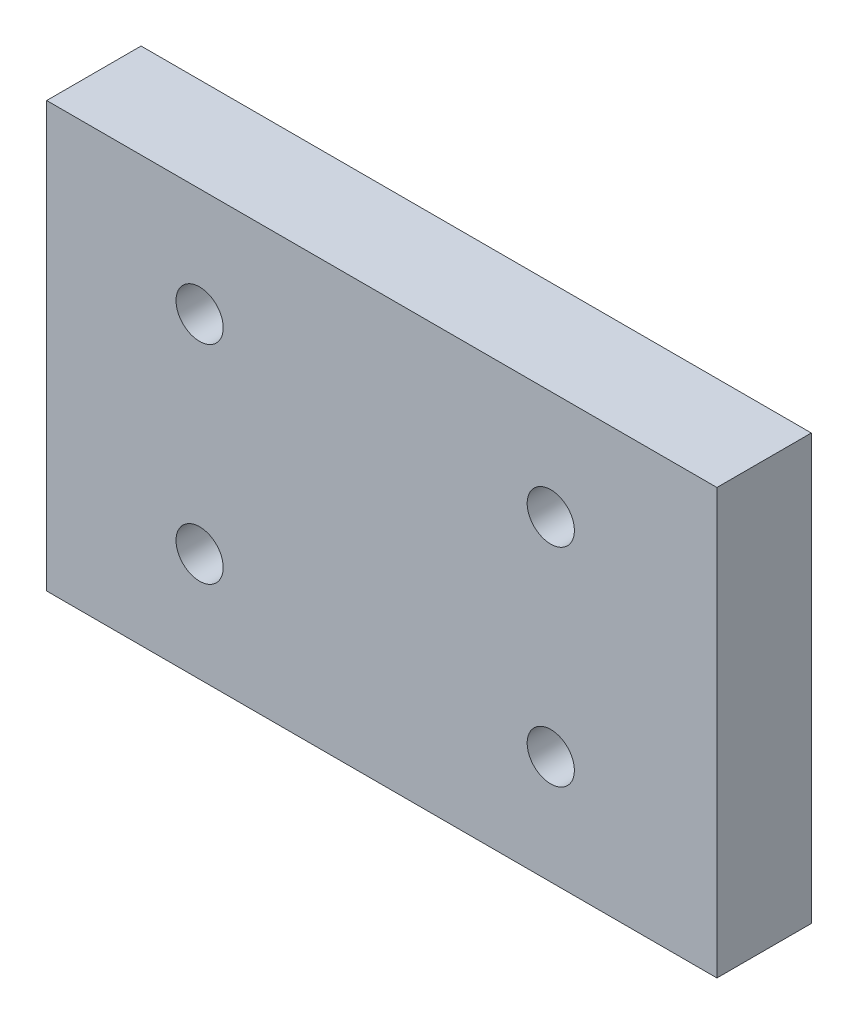
SolidWorks part; units mm, degrees
ref_plane "Front Plane" through (0, 0, 0) normal (0, 0, 1) x (1, 0, 0)
ref_plane "Top Plane" through (0, 0, 0) normal (0, 1, 0) x (1, 0, 0)
ref_plane "Right Plane" through (0, 0, 0) normal (1, 0, 0) x (0, 0, -1)
sketch "Sketch1" plane through (0, 0, 0) normal (0, 0, 1) x (1, 0, 0)
  line L0 (0, 0) -> (0, 25) construction
  line L1 (51, 25) -> (0, 25)
  line L2 (51, 25) -> (51, 0)
  line L3 (51, 0) -> (0, 0)
  line L4 (0, 25) -> (0, 0)
  line L5 (51, 4.5) -> (51, 20.5) construction
  line L6 (21.1, 25) -> (22.3, 25) construction
  line L7 (21.1, 0) -> (22.3, 0) construction
  line L8 (61, 35) -> (61, -10)
  line L9 (61, -10) -> (-10, -10)
  line L10 (-10, 35) -> (-10, -10)
  line L11 (61, 35) -> (-10, 35)
  circle A0 centre (43.4, 1.5) radius 2.5
  circle A1 centre (6.2, 1.5) radius 2.5
  circle A2 centre (43.4, 23.5) radius 2.5
  circle A3 centre (6.2, 23.5) radius 2.5
  dimension "D2" = 5
  dimension "D1" = 10
extrude "Boss-Extrude1" add sketch "Sketch1" along normal blind 10 contours L8 L11 L10 L9 A3 L1 A2 L2 L3 A0 A1 L4 | A3 L1 L4 L3 A1 A0 L2 A2
